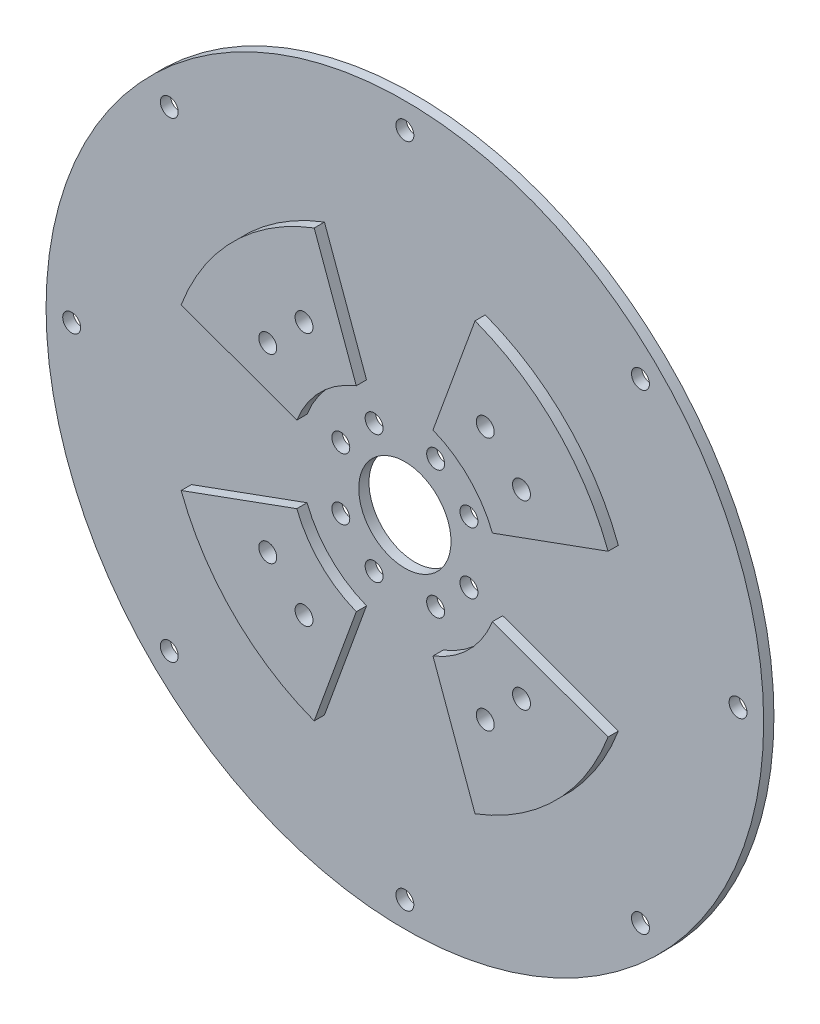
SolidWorks part; units mm, degrees
ref_plane "Front Plane" through (0, 0, 0) normal (0, 0, 1) x (1, 0, 0)
ref_plane "Top Plane" through (0, 0, 0) normal (0, 1, 0) x (1, 0, 0)
ref_plane "Right Plane" through (0, 0, 0) normal (1, 0, 0) x (0, 0, -1)
sketch "Sketch1" plane through (0, 0, 0) normal (0, 0, 1) x (1, 0, 0)
  circle A0 centre (0, 0) radius 70
  circle A1 centre (0, 0) radius 9
  dimension "D1" = 140
  dimension "D2" = 18
extrude "Boss-Extrude1" add sketch "Sketch1" along normal blind 2
sketch "Sketch2" plane through (0, 0, 2) normal (0, 0, 1) x (1, 0, 0)
  line L2 (0, 0) -> (0, 38.5988) construction
  line L3 (0, 0) -> (38.5988, 0) construction
  line L4 (7.4792, 19.087) -> (15.6888, 41.6427)
  line L5 (19.087, 7.4792) -> (41.6427, 15.6888)
  arc A0 (19.087, 7.4792) -> (7.4792, 19.087) centre (0, 0) ccw
  arc A1 (41.6427, 15.6888) -> (15.6888, 41.6427) centre (0, 0) ccw
  dimension "D5" = 20.5
  dimension "D6" = 44.5
extrude "Boss-Extrude2" add sketch "Sketch2" along normal blind 2
sketch "Sketch5" plane through (0, 0, 4) normal (0, 0, 1) x (1, 0, 0)
  line L0 (0, 0) -> (31.4663, 31.4663) construction
  line L1 (17.6777, 24.7487) -> (24.7487, 17.6777) construction
  arc A0 (41.6427, 15.6888) -> (15.6888, 41.6427) centre (0, 0) ccw construction
  circle A1 centre (17.6777, 24.7487) radius 1.75
  circle A2 centre (24.7487, 17.6777) radius 1.75
  point P9 (21.2132, 21.2132)
  dimension "D2" = 3.5
  dimension "D3" = 3.5
  dimension "D1" = 10
  dimension "D4" = 30
extrude "Cut-Extrude4" cut sketch "Sketch5" against normal through all
pattern_circular "CirPattern1" count 4 every 90 about axis through (0, 0, 0) along (0, 0, 1) of "Boss-Extrude2", "Cut-Extrude4"
sketch "Sketch3" plane through (0, 0, 2) normal (0, 0, 1) x (1, 0, 0)
  line L0 (-12.5, 6) -> (12.5, 6) construction
  line L1 (12.5, 6) -> (12.5, -6) construction
  line L2 (12.5, -6) -> (-12.5, 6) construction
  line L3 (-12.5, 6) -> (-12.5, -6) construction
  line L4 (-12.5, -6) -> (12.5, -6) construction
  circle A0 centre (-12.5, 6) radius 1.75
  circle A1 centre (12.5, 6) radius 1.75
  circle A2 centre (12.5, -6) radius 1.75
  circle A3 centre (-12.5, -6) radius 1.75
  point P3 (0, 0)
  dimension "D3" = 3.5
  dimension "D4" = 3.5
  dimension "D5" = 3.5
  dimension "D6" = 3.5
  dimension "D1" = 25
  dimension "D2" = 12
extrude "Cut-Extrude2" cut sketch "Sketch3" against normal through all
pattern_circular "CirPattern2" count 2 every 90 about axis through (0, 0, 0) along (0, 0, 1) of "Cut-Extrude2"
sketch "Sketch4" plane through (0, 0, 2) normal (0, 0, 1) x (1, 0, 0)
  line L0 (0, 65) -> (0, 70) construction
  circle A0 centre (0, 65) radius 1.75
  circle A1 centre (0, 0) radius 70 construction
  dimension "D2" = 3.5
  dimension "D1" = 5
extrude "Cut-Extrude3" cut sketch "Sketch4" against normal through all
pattern_circular "CirPattern3" count 8 every 45 about axis through (0, 0, 0) along (0, 0, 1) of "Cut-Extrude3"
